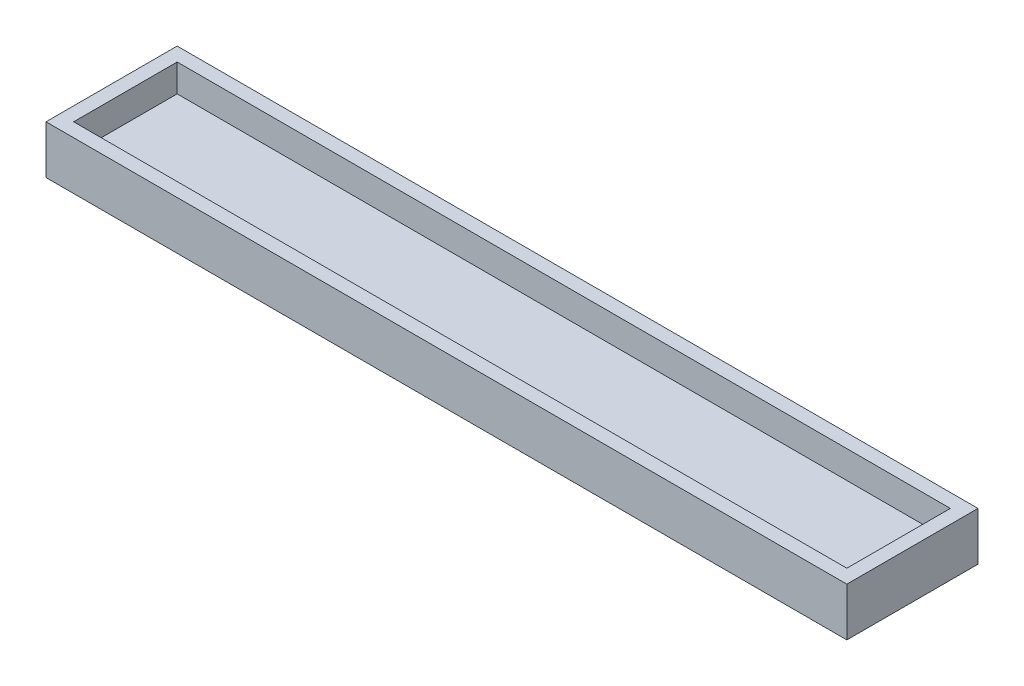
SolidWorks part; units mm, degrees
ref_plane "前视基准面" through (0, 0, 0) normal (0, 0, 1) x (1, 0, 0)
ref_plane "上视基准面" through (0, 0, 0) normal (0, 1, 0) x (1, 0, 0)
ref_plane "右视基准面" through (0, 0, 0) normal (1, 0, 0) x (0, 0, -1)
other "Configuration Table"
sketch "草图1" plane through (0, 0, 0) normal (0, 1, 0) x (1, 0, 0)
  line L1 (0, 0) -> (112, 0)
  line L2 (0, 0) -> (0, -15)
  line L3 (0, -15) -> (112, -15)
  line L4 (112, 0) -> (112, -15)
  dimension "D1" = 112
  dimension "D2" = 15
extrude "凸台-拉伸1" add sketch "草图1" along normal blind 3 contours L2 L1 L4 L3
sketch "草图2" plane through (0, 0, 0) normal (0, -1, 0) x (1, 0, 0)
  line L0 (-2, 17) -> (-2, -2)
  line L1 (0, 15) -> (112, 15)
  line L2 (0, 15) -> (0, 0)
  line L3 (0, 0) -> (112, 0)
  line L4 (112, 15) -> (112, 0)
  line L5 (-2, -2) -> (114, -2)
  line L6 (114, 17) -> (114, -2)
  line L7 (-2, 17) -> (114, 17)
  dimension "D1" = 2
extrude "凸台-拉伸2" add sketch "草图2" against normal blind 7 contours L0 L5 L6 L7 | L2 L1 L4 L3
